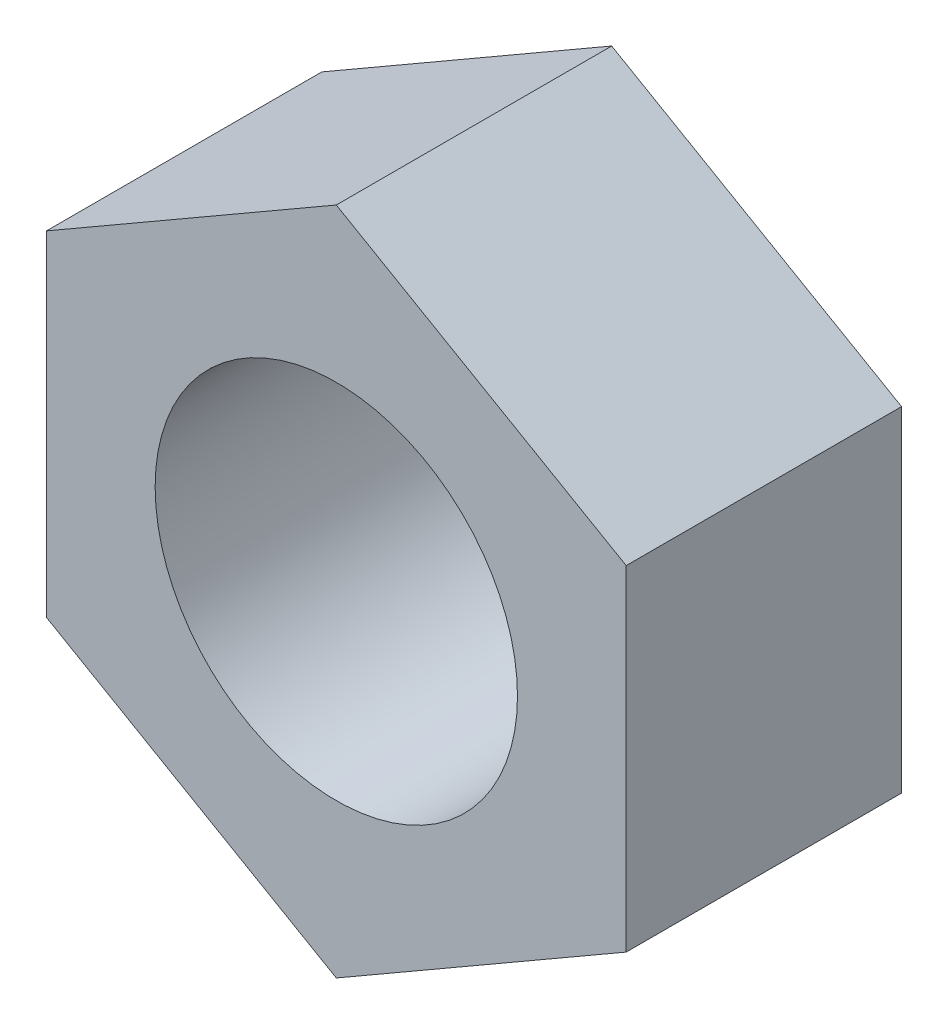
SolidWorks part; units mm, degrees
ref_plane "Front Plane" through (0, 0, 0) normal (0, 0, 1) x (1, 0, 0)
ref_plane "Top Plane" through (0, 0, 0) normal (0, 1, 0) x (1, 0, 0)
ref_plane "Right Plane" through (0, 0, 0) normal (1, 0, 0) x (0, 0, -1)
sketch "Sketch1" plane through (0, 0, 0) normal (0, 0, 1) x (1, 0, 0)
  line L1 (0, 4.6188) -> (-4, 2.3094)
  line L2 (-4, 2.3094) -> (-4, -2.3094)
  line L3 (-4, -2.3094) -> (0, -4.6188)
  line L4 (0, -4.6188) -> (4, -2.3094)
  line L5 (4, -2.3094) -> (4, 2.3094)
  line L6 (4, 2.3094) -> (0, 4.6188)
  circle A0 centre (0, 0) radius 4 construction
  circle A1 centre (0, 0) radius 2.5
  dimension "D2" = 5
  dimension "D1" = 8
extrude "Boss-Extrude1" add sketch "Sketch1" along normal blind 3.8
